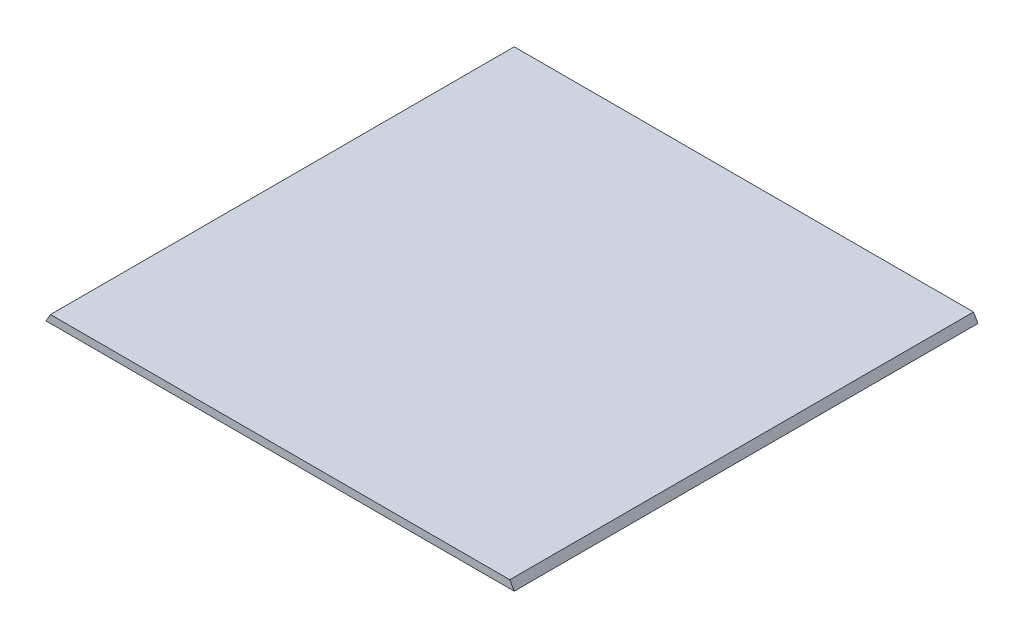
SolidWorks part; units mm, degrees
ref_plane "Front Plane" through (0, 0, 0) normal (0, 0, 1) x (1, 0, 0)
ref_plane "Top Plane" through (0, 0, 0) normal (0, 1, 0) x (1, 0, 0)
ref_plane "Right Plane" through (0, 0, 0) normal (1, 0, 0) x (0, 0, -1)
sketch "Sketch1" plane through (0, 0, 0) normal (0, 1, 0) x (1, 0, 0)
  line L1 (0, 0) -> (381, 0)
  line L2 (0, 0) -> (0, -381)
  line L3 (0, -381) -> (381, -381)
  line L4 (381, 0) -> (381, -381)
extrude "Boss-Extrude1" add sketch "Sketch1" along normal blind 6.35
sketch "Sketch2" plane through (0, 0, 381) normal (0, 0, 1) x (1, 0, 0)
  line L0 (0, 0) -> (3.6662, 6.35)
  line L1 (0, 6.35) -> (381, 6.35) construction
  line L2 (3.6662, 6.35) -> (0, 6.35)
  line L3 (0, 6.35) -> (0, 0) construction
  line L4 (0, 6.35) -> (0, 0)
  arc A0 (0, 2.7423) -> (1.3711, 2.3749) centre (0, 0) cw construction
extrude "Cut-Extrude1" cut sketch "Sketch2" against normal through all
sketch "Sketch5" plane through (0, 0, 381) normal (0, 0, 1) x (1, 0, 0)
  line L0 (381, 0) -> (384.6662, 0)
  line L1 (384.6662, 0) -> (381, 6.35)
  line L2 (3.6662, 6.35) -> (0, 6.35) construction
  line L3 (381, 6.35) -> (381, 0)
extrude "Boss-Extrude2" add sketch "Sketch5" against normal up to surface (381 mm away) up to face at (191.4165, 3.175, 0)
